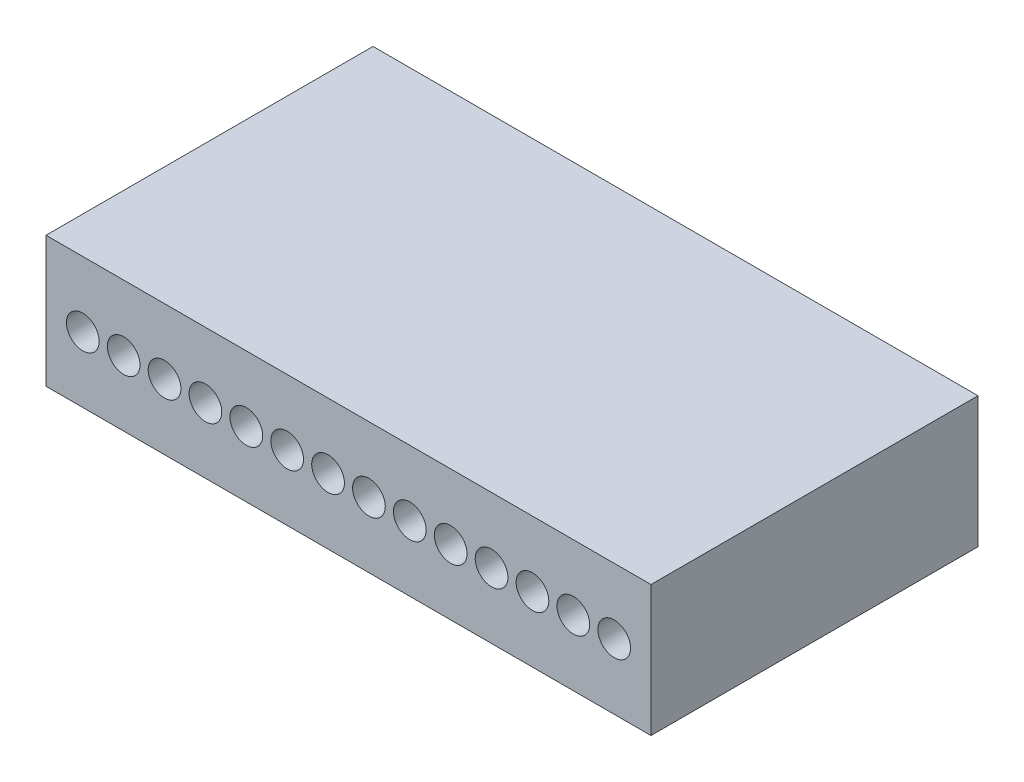
SolidWorks part; units mm, degrees
ref_plane "Front Plane" through (0, 0, 0) normal (0, 0, 1) x (1, 0, 0)
ref_plane "Top Plane" through (0, 0, 0) normal (0, 1, 0) x (1, 0, 0)
ref_plane "Right Plane" through (0, 0, 0) normal (1, 0, 0) x (0, 0, -1)
sketch "Sketch2" plane through (0, 0, 0) normal (0, 0, 1) x (1, 0, 0)
  line L1 (0, 0) -> (18.5, 0)
  line L2 (0, 0) -> (0, 4)
  line L3 (0, 4) -> (18.5, 4)
  line L4 (18.5, 0) -> (18.5, 4)
  dimension "D1" = 18.5
  dimension "D2" = 4
extrude "Boss-Extrude1" add sketch "Sketch2" along normal blind 10
sketch "Sketch3" plane through (0, 0, 10) normal (0, 0, 1) x (1, 0, 0)
  line L0 (0, 2) -> (18.5, 2) construction
  line L1 (0, 4) -> (0, 0) construction
  line L2 (18.5, 0) -> (18.5, 4) construction
  line L3 (0, 2) -> (18.5, 2) construction
  line L4 (18.5, 4) -> (0, 4) construction
  line L5 (0, 0) -> (18.5, 0) construction
  line L6 (1.125, 4) -> (1.125, 0) construction
  circle A0 centre (1.125, 2) radius 0.5
  circle A1 centre (2.375, 2) radius 0.5
  circle A2 centre (3.625, 2) radius 0.5
  circle A3 centre (4.875, 2) radius 0.5
  circle A4 centre (6.125, 2) radius 0.5
  circle A5 centre (7.375, 2) radius 0.5
  circle A6 centre (8.625, 2) radius 0.5
  circle A7 centre (9.875, 2) radius 0.5
  circle A8 centre (11.125, 2) radius 0.5
  circle A9 centre (12.375, 2) radius 0.5
  circle A10 centre (13.625, 2) radius 0.5
  circle A11 centre (14.875, 2) radius 0.5
  circle A12 centre (16.125, 2) radius 0.5
  circle A13 centre (17.375, 2) radius 0.5
  circle A21 centre (24.875, 2) radius 0.5 [skipped]
  circle A22 centre (23.625, 2) radius 0.5 [skipped]
  circle A23 centre (22.375, 2) radius 0.5 [skipped]
  circle A24 centre (21.125, 2) radius 0.5 [skipped]
  circle A25 centre (19.875, 2) radius 0.5 [skipped]
  circle A26 centre (18.625, 2) radius 0.5 [skipped]
  dimension "D1" = 1
  dimension "D2" = 2
  dimension "D3" = 1.125
  dimension "D5" = 1.25
  dimension "D4" = 20
extrude "Cut-Extrude1" cut sketch "Sketch3" against normal blind 5
sketch "Sketch4" plane through (0, 0, 10) normal (0, 0, 1) x (1, 0, 0)
  point P0 (1.125, 2)
  point P1 (2.375, 2)
  point P3 (3.625, 2)
  point P5 (4.875, 2)
  point P7 (6.125, 2)
  point P9 (7.375, 2)
  point P11 (8.625, 2)
  point P13 (9.875, 2)
  point P15 (11.125, 2)
  point P17 (12.375, 2)
  point P19 (13.625, 2)
  point P21 (14.875, 2)
  point P23 (16.125, 2)
  point P25 (17.375, 2)
  point P37 (0, 0)
